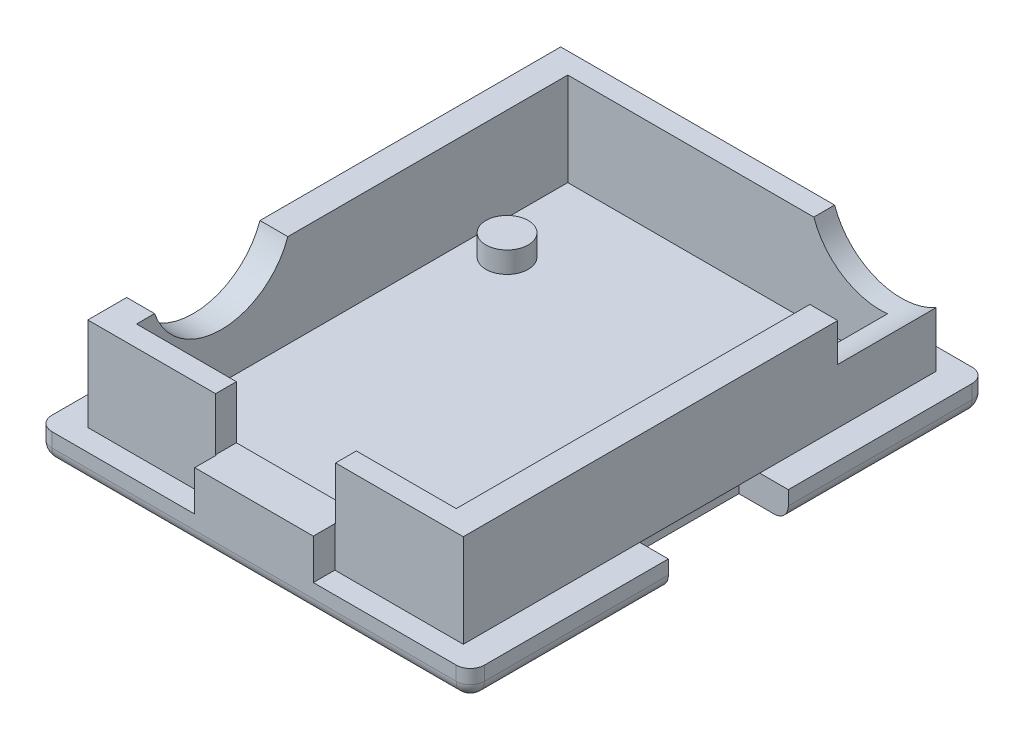
SolidWorks part; units mm, degrees
ref_plane "Front Plane" through (0, 0, 0) normal (0, 0, 1) x (1, 0, 0)
ref_plane "Top Plane" through (0, 0, 0) normal (0, 1, 0) x (1, 0, 0)
ref_plane "Right Plane" through (0, 0, 0) normal (1, 0, 0) x (0, 0, -1)
sketch "Sketch1" plane through (0, 0.8, 0) normal (0, 1, 0) x (1, 0, 0)
  circle A0 centre (-8.9, -13.05) radius 1
  circle A1 centre (-8.9, 8.55) radius 1
  circle A2 centre (8.9, 8.55) radius 1
  circle A3 centre (8.9, -13.05) radius 1
  dimension "D1" = 2
extrude "Boss-Extrude1" add sketch "Sketch1" against normal up to surface (1.6 mm away)
sketch "Sketch2" plane through (0, -0.8, 0) normal (0, -1, 0) x (1, 0, 0)
  circle A0 centre (-8.9, -8.55) radius 1.5
  circle A1 centre (-8.9, 13.05) radius 1.5
  circle A2 centre (8.9, 13.05) radius 1.5
  circle A3 centre (8.9, -8.55) radius 1.5
  dimension "D1" = 3
extrude "Boss-Extrude2" add sketch "Sketch2" along normal up to surface (1.5 mm away)
sketch "Sketch3" plane through (0, -2.3, 0) normal (0, -1, 0) x (1, 0, 0)
  line L0 (0, -2.0264) -> (0, 0) construction
  line L1 (-15.325, 18.275) -> (15.325, 18.275)
  line L2 (-15.325, 18.275) -> (-15.325, 4.25)
  line L3 (-15.325, -18.275) -> (15.325, -18.275)
  line L4 (15.325, 18.275) -> (15.325, 4.25)
  line L5 (-15.325, 18.275) -> (15.325, -18.275) construction
  line L6 (-15.325, -18.275) -> (15.325, 18.275) construction
  line L7 (11.175, -15.125) -> (-11.175, -15.125) construction
  line L8 (0, -15.125) -> (0, -18.275) construction
  line L9 (0, 18.275) -> (0, 15.125) construction
  line L10 (-11.175, 15.125) -> (11.175, 15.125) construction
  line L11 (-11.175, 0) -> (-15.325, 0) construction
  line L12 (-11.175, -15.125) -> (-11.175, 15.125) construction
  line L13 (11.175, 0) -> (15.325, 0) construction
  line L15 (15.325, -4.25) -> (15.325, -18.275)
  line L16 (-11.825, -4.25) -> (-15.325, -4.25)
  line L17 (-11.825, -4.25) -> (-11.825, 4.25)
  line L18 (-11.825, 4.25) -> (-15.325, 4.25)
  line L20 (-11.825, -4.25) -> (-15.325, 4.25) construction
  line L21 (-11.825, 4.25) -> (-15.325, -4.25) construction
  line L22 (11.825, -4.25) -> (15.325, -4.25)
  line L23 (11.825, -4.25) -> (11.825, 4.25)
  line L24 (11.825, 4.25) -> (15.325, 4.25)
  line L26 (11.825, -4.25) -> (15.325, 4.25) construction
  line L27 (11.825, 4.25) -> (15.325, -4.25) construction
  line L28 (-15.325, -4.25) -> (-15.325, -18.275)
  line L29 (-15.325, 4.25) -> (-15.325, -4.25) construction
  line L30 (15.325, -4.25) -> (15.325, 4.25) construction
  line L31 (11.175, 15.125) -> (11.175, -15.125) construction
  point P0 (0, 0)
  point P24 (-13.575, 0)
  point P29 (13.575, 0)
  dimension "D1" = 4.15
  dimension "D2" = 3.15
  dimension "D3" = 3.5
  dimension "D4" = 8.5
extrude "Boss-Extrude3" add sketch "Sketch3" along normal blind 2
sketch "Sketch4" plane through (0, -2.3, 0) normal (0, 1, 0) x (1, 0, 0)
  line L5 (-11.325, -15.275) -> (11.325, -15.275)
  line L6 (-11.325, -15.275) -> (-11.325, 15.275)
  line L7 (-11.325, 15.275) -> (11.325, 15.275)
  line L8 (-11.175, -15.125) -> (11.175, 15.125) construction
  line L9 (11.325, -15.275) -> (11.325, 15.275)
  line L10 (-11.325, -15.275) -> (11.325, 15.275) construction
  line L11 (-11.325, 15.275) -> (11.325, -15.275) construction
  line L12 (-13.3, -16.75) -> (-4.2, -16.75)
  line L13 (-13.3, -16.75) -> (-13.3, -4.5)
  line L14 (-13.3, 16.75) -> (13.3, 16.75)
  line L15 (13.3, -16.75) -> (13.3, -4.5)
  line L16 (-13.3, -16.75) -> (13.3, 16.75) construction
  line L17 (-13.3, 16.75) -> (13.3, -16.75) construction
  line L20 (-13.3, -4.5) -> (-13.8, -4.5) construction
  line L22 (-13.3, 4.5) -> (-13.8, 4.5) construction
  line L23 (-13.8, -4.5) -> (-13.8, 4.5) construction
  line L25 (13.3, 4.5) -> (13.8, 4.5) construction
  line L27 (13.3, -4.5) -> (13.8, -4.5) construction
  line L28 (13.8, 4.5) -> (13.8, -4.5) construction
  line L29 (-13.3, 4.5) -> (-13.3, 16.75)
  line L30 (13.3, 4.5) -> (13.3, 16.75)
  line L32 (0, -18.275) -> (0, -15.275) construction
  line L33 (-13.8, 0) -> (-11.825, 0) construction
  line L34 (-11.825, -4.25) -> (-11.825, 4.25) construction
  line L35 (-4.2, -18.275) -> (4.2, -18.275)
  line L36 (-4.2, -18.275) -> (-4.2, -16.75)
  line L38 (4.2, -18.275) -> (4.2, -16.75)
  line L39 (-15.325, 18.275) -> (15.325, 18.275) construction
  line L40 (-15.325, 4.25) -> (-15.325, 18.275) construction
  line L41 (15.325, -18.275) -> (-15.325, -18.275) construction
  line L42 (4.2, -16.75) -> (13.3, -16.75)
  line L43 (-13.3, 4.5) -> (-13.3, -4.5)
  line L44 (13.3, -4.5) -> (13.3, 4.5)
  point P0 (0, 0)
  point P5 (0, 0)
  dimension "D1" = 1.525
  dimension "D2" = 2.025
  dimension "D3" = 1.475
  dimension "D4" = 1.975
  dimension "D5" = 0.5
  dimension "D6" = 9
  dimension "D7" = 8.4
extrude "Boss-Extrude4" add sketch "Sketch4" along normal offset from surface (6.6 mm away) 3.5
sketch "Sketch5" plane through (0, 4.3, 0) normal (0, 1, 0) x (1, 0, 0)
  line L0 (4.25, -18.275) -> (-4.25, -18.275)
  line L1 (4.25, -18.275) -> (4.25, -15.275)
  line L2 (-4.25, -18.275) -> (-4.25, -15.275)
  line L3 (4.25, -15.275) -> (-4.25, -15.275)
  line L4 (11.325, -15.275) -> (-11.325, -15.275) construction
  line L5 (0, -18.275) -> (0, -15.275) construction
  line L6 (4.2, -18.275) -> (-4.2, -18.275) construction
  dimension "D1" = 8.5
extrude "Cut-Extrude1" cut sketch "Sketch5" against normal offset from surface (3.75 mm away) 0.25
fillet "Fillet1" radius 1 10 edges at (0, -4.3, -18.275) (-15.325, -4.3, -11.2625) (-15.325, -4.3, 11.2625) (0, -4.3, 18.275) (15.325, -4.3, 11.2625) (15.325, -4.3, -11.2625) (15.325, -3.3, 18.275) (15.325, -3.3, -18.275) (-15.325, -3.3, -18.275) (-15.325, -3.3, 18.275)
sketch "Sketch6" plane through (-7.325, 0, 0) normal (1, 0, 0) x (0, 0, -1)
  circle A0 centre (-9.275, 5.95) radius 5
  arc A1 (-13.0167, 8.45) -> (-5.5333, 8.45) centre (-9.275, 5.95) ccw construction
  dimension "D1" = 0.5
extrude "Cut-Extrude2" cut sketch "Sketch6" against normal through all
sketch "Sketch8" plane through (0, 0, -10.275) normal (0, 0, 1) x (1, 0, 0)
  circle A0 centre (10.825, 5.95) radius 5
  arc A1 (7.0833, 8.45) -> (13.35, 2.2252) centre (10.825, 5.95) ccw construction
  dimension "D1" = 0.5
extrude "Cut-Extrude3" cut sketch "Sketch8" against normal through all and the other way blind 0.5
sketch "Sketch9" plane through (0, 0.8, 0) normal (0, 1, 0) x (1, 0, 0)
  line L1 (-11.325, 15.275) -> (11.325, 15.275)
  line L2 (-11.325, 15.275) -> (-11.325, -15.275)
  line L3 (-11.325, -15.275) -> (11.325, -15.275)
  line L4 (11.325, 15.275) -> (11.325, -15.275)
extrude "Cut-Extrude4" cut sketch "Sketch9" against normal up to surface (1.6 mm away) up to face at (-8.9, -0.8, -9.55)
